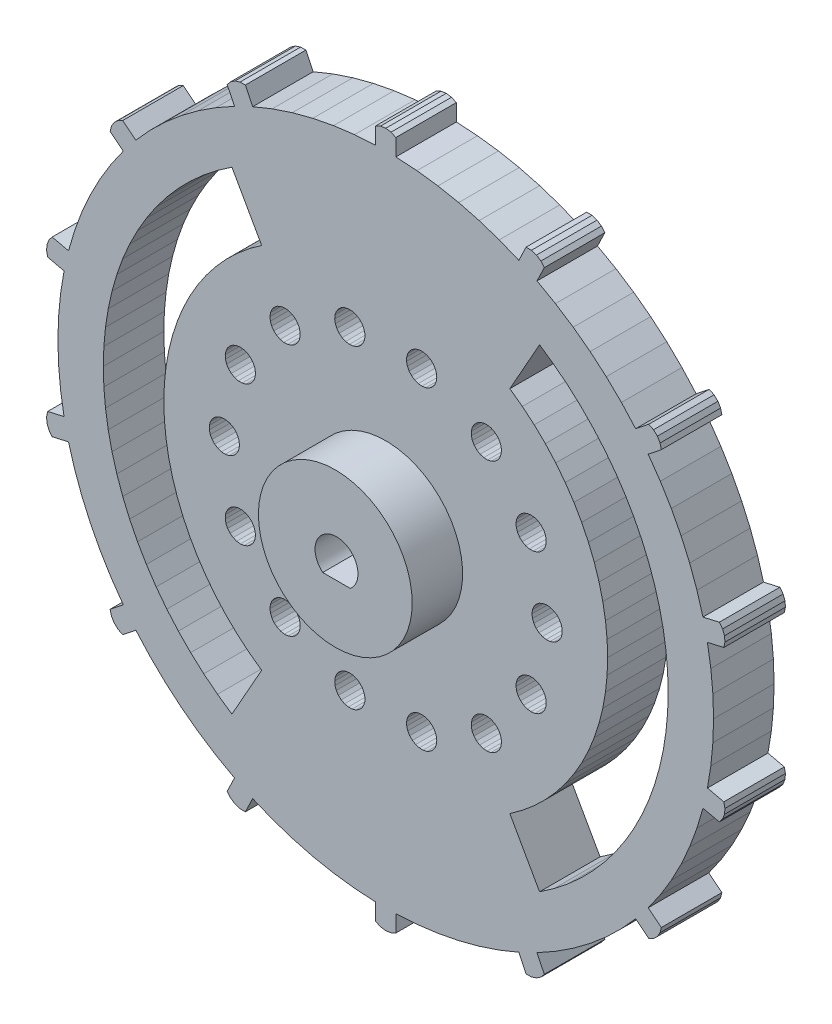
SolidWorks part; units mm, degrees
ref_plane "Front Plane" through (0, 0, 0) normal (0, 0, 1) x (1, 0, 0)
ref_plane "Top Plane" through (0, 0, 0) normal (0, 1, 0) x (1, 0, 0)
ref_plane "Right Plane" through (0, 0, 0) normal (1, 0, 0) x (0, 0, -1)
ref_plane "Plane1" through (0, 0, 6) normal (0, 0, 1) x (1, 0, 0)
sketch "Sketch1" plane through (0, 0, 6) normal (0, 0, 1) x (1, 0, 0)
  line L0 (26.5481, -21.8385) -> (26.9325, -21.478)
  line L1 (26.9325, -21.478) -> (27.1985, -21.023)
  line L2 (27.1985, -21.023) -> (27.3239, -20.5111)
  line L3 (27.3239, -20.5111) -> (26.021, -19.472)
  line L4 (26.021, -19.472) -> (27.2227, -17.7532)
  line L5 (27.2227, -17.7532) -> (28.311, -15.9604)
  line L6 (28.311, -15.9604) -> (29.2815, -14.1012)
  line L7 (29.2815, -14.1012) -> (30.13, -12.1833)
  line L8 (30.13, -12.1833) -> (30.8531, -10.2146)
  line L9 (30.8531, -10.2146) -> (31.4476, -8.2034)
  line L10 (31.4476, -8.2034) -> (33.0724, -8.5743)
  line L11 (33.0724, -8.5743) -> (33.3944, -8.157)
  line L12 (33.3944, -8.157) -> (33.5843, -7.6654)
  line L13 (33.5843, -7.6654) -> (33.6265, -7.1401)
  line L14 (33.6265, -7.1401) -> (33.5174, -6.6244)
  line L15 (33.5174, -6.6244) -> (31.8927, -6.2536)
  line L16 (31.8927, -6.2536) -> (32.2296, -4.1836)
  line L17 (32.2296, -4.1836) -> (32.4323, -2.0962)
  line L18 (32.4323, -2.0962) -> (32.5, 0)
  line L19 (32.5, 0) -> (32.4323, 2.0962)
  line L20 (32.4323, 2.0962) -> (32.2296, 4.1836)
  line L21 (32.2296, 4.1836) -> (31.8927, 6.2536)
  line L22 (31.8927, 6.2536) -> (33.5174, 6.6244)
  line L23 (33.5174, 6.6244) -> (33.6265, 7.1401)
  line L24 (33.6265, 7.1401) -> (33.5843, 7.6654)
  line L25 (33.5843, 7.6654) -> (33.3944, 8.157)
  line L26 (33.3944, 8.157) -> (33.0724, 8.5743)
  line L27 (33.0724, 8.5743) -> (31.4476, 8.2034)
  line L28 (31.4476, 8.2034) -> (30.8531, 10.2146)
  line L29 (30.8531, 10.2146) -> (30.13, 12.1833)
  line L30 (30.13, 12.1833) -> (29.2815, 14.1012)
  line L31 (29.2815, 14.1012) -> (28.311, 15.9604)
  line L32 (28.311, 15.9604) -> (27.2227, 17.7532)
  line L33 (27.2227, 17.7532) -> (26.021, 19.472)
  line L34 (26.021, 19.472) -> (27.3239, 20.5111)
  line L35 (27.3239, 20.5111) -> (27.1985, 21.023)
  line L36 (27.1985, 21.023) -> (26.9325, 21.478)
  line L37 (26.9325, 21.478) -> (26.5481, 21.8385)
  line L38 (26.5481, 21.8385) -> (26.077, 22.0747)
  line L39 (26.077, 22.0747) -> (24.774, 21.0357)
  line L40 (24.774, 21.0357) -> (23.3657, 22.5897)
  line L41 (23.3657, 22.5897) -> (21.8601, 24.0497)
  line L42 (21.8601, 24.0497) -> (20.2634, 25.4095)
  line L43 (20.2634, 25.4095) -> (18.5824, 26.6635)
  line L44 (18.5824, 26.6635) -> (16.824, 27.8065)
  line L45 (16.824, 27.8065) -> (14.9955, 28.8337)
  line L46 (14.9955, 28.8337) -> (15.7186, 30.3353)
  line L47 (15.7186, 30.3353) -> (15.3835, 30.742)
  line L48 (15.3835, 30.742) -> (14.9464, 31.0366)
  line L49 (14.9464, 31.0366) -> (14.4436, 31.1946)
  line L50 (14.4436, 31.1946) -> (13.9167, 31.203)
  line L51 (13.9167, 31.203) -> (13.1936, 29.7015)
  line L52 (13.1936, 29.7015) -> (11.2504, 30.4906)
  line L53 (11.2504, 30.4906) -> (9.2605, 31.1527)
  line L54 (9.2605, 31.1527) -> (7.2319, 31.6852)
  line L55 (7.2319, 31.6852) -> (5.1733, 32.0856)
  line L56 (5.1733, 32.0856) -> (3.0931, 32.3525)
  line L57 (3.0931, 32.3525) -> (1, 32.4846)
  line L58 (1, 32.4846) -> (1, 34.1512)
  line L59 (1, 34.1512) -> (0.5216, 34.3722)
  line L60 (0.5216, 34.3722) -> (0, 34.448)
  line L61 (0, 34.448) -> (-0.5216, 34.3722)
  line L62 (-0.5216, 34.3722) -> (-1, 34.1512)
  line L63 (-1, 34.1512) -> (-1, 32.4846)
  line L64 (-1, 32.4846) -> (-3.0931, 32.3525)
  line L65 (-3.0931, 32.3525) -> (-5.1733, 32.0856)
  line L66 (-5.1733, 32.0856) -> (-7.2319, 31.6852)
  line L67 (-7.2319, 31.6852) -> (-9.2605, 31.1527)
  line L68 (-9.2605, 31.1527) -> (-11.2504, 30.4906)
  line L69 (-11.2504, 30.4906) -> (-13.1936, 29.7015)
  line L70 (-13.1936, 29.7015) -> (-13.9167, 31.203)
  line L71 (-13.9167, 31.203) -> (-14.4436, 31.1946)
  line L72 (-14.4436, 31.1946) -> (-14.9464, 31.0366)
  line L73 (-14.9464, 31.0366) -> (-15.3835, 30.742)
  line L74 (-15.3835, 30.742) -> (-15.7186, 30.3353)
  line L75 (-15.7186, 30.3353) -> (-14.9955, 28.8337)
  line L76 (-14.9955, 28.8337) -> (-16.824, 27.8065)
  line L77 (-16.824, 27.8065) -> (-18.5824, 26.6635)
  line L78 (-18.5824, 26.6635) -> (-20.2634, 25.4095)
  line L79 (-20.2634, 25.4095) -> (-21.8601, 24.0497)
  line L80 (-21.8601, 24.0497) -> (-23.3657, 22.5897)
  line L81 (-23.3657, 22.5897) -> (-24.774, 21.0357)
  line L82 (-24.774, 21.0357) -> (-26.077, 22.0747)
  line L83 (-26.077, 22.0747) -> (-26.5481, 21.8385)
  line L84 (-26.5481, 21.8385) -> (-26.9325, 21.478)
  line L85 (-26.9325, 21.478) -> (-27.1985, 21.023)
  line L86 (-27.1985, 21.023) -> (-27.3239, 20.5111)
  line L87 (-27.3239, 20.5111) -> (-26.021, 19.472)
  line L88 (-26.021, 19.472) -> (-27.2227, 17.7532)
  line L89 (-27.2227, 17.7532) -> (-28.311, 15.9604)
  line L90 (-28.311, 15.9604) -> (-29.2815, 14.1012)
  line L91 (-29.2815, 14.1012) -> (-30.13, 12.1833)
  line L92 (-30.13, 12.1833) -> (-30.8531, 10.2146)
  line L93 (-30.8531, 10.2146) -> (-31.4476, 8.2034)
  line L94 (-31.4476, 8.2034) -> (-33.0724, 8.5743)
  line L95 (-33.0724, 8.5743) -> (-33.3944, 8.157)
  line L96 (-33.3944, 8.157) -> (-33.5843, 7.6654)
  line L97 (-33.5843, 7.6654) -> (-33.6265, 7.1401)
  line L98 (-33.6265, 7.1401) -> (-33.5174, 6.6244)
  line L99 (-33.5174, 6.6244) -> (-31.8927, 6.2536)
  line L100 (-31.8927, 6.2536) -> (-32.2296, 4.1836)
  line L101 (-32.2296, 4.1836) -> (-32.4323, 2.0962)
  line L102 (-32.4323, 2.0962) -> (-32.5, 0)
  line L103 (-32.5, 0) -> (-32.4323, -2.0962)
  line L104 (-32.4323, -2.0962) -> (-32.2296, -4.1836)
  line L105 (-32.2296, -4.1836) -> (-31.8927, -6.2536)
  line L106 (-31.8927, -6.2536) -> (-33.5174, -6.6244)
  line L107 (-33.5174, -6.6244) -> (-33.6265, -7.1401)
  line L108 (-33.6265, -7.1401) -> (-33.5843, -7.6654)
  line L109 (-33.5843, -7.6654) -> (-33.3944, -8.157)
  line L110 (-33.3944, -8.157) -> (-33.0724, -8.5743)
  line L111 (-33.0724, -8.5743) -> (-31.4476, -8.2034)
  line L112 (-31.4476, -8.2034) -> (-30.8531, -10.2146)
  line L113 (-30.8531, -10.2146) -> (-30.13, -12.1833)
  line L114 (-30.13, -12.1833) -> (-29.2815, -14.1012)
  line L115 (-29.2815, -14.1012) -> (-28.311, -15.9604)
  line L116 (-28.311, -15.9604) -> (-27.2227, -17.7532)
  line L117 (-27.2227, -17.7532) -> (-26.021, -19.472)
  line L118 (-26.021, -19.472) -> (-27.3239, -20.5111)
  line L119 (-27.3239, -20.5111) -> (-27.1985, -21.023)
  line L120 (-27.1985, -21.023) -> (-26.9325, -21.478)
  line L121 (-26.9325, -21.478) -> (-26.5481, -21.8385)
  line L122 (-26.5481, -21.8385) -> (-26.077, -22.0747)
  line L123 (-26.077, -22.0747) -> (-24.774, -21.0357)
  line L124 (-24.774, -21.0357) -> (-23.3657, -22.5897)
  line L125 (-23.3657, -22.5897) -> (-21.8601, -24.0497)
  line L126 (-21.8601, -24.0497) -> (-20.2634, -25.4095)
  line L127 (-20.2634, -25.4095) -> (-18.5824, -26.6635)
  line L128 (-18.5824, -26.6635) -> (-16.824, -27.8065)
  line L129 (-16.824, -27.8065) -> (-14.9955, -28.8337)
  line L130 (-14.9955, -28.8337) -> (-15.7186, -30.3353)
  line L131 (-15.7186, -30.3353) -> (-15.3835, -30.742)
  line L132 (-15.3835, -30.742) -> (-14.9464, -31.0366)
  line L133 (-14.9464, -31.0366) -> (-14.4436, -31.1946)
  line L134 (-14.4436, -31.1946) -> (-13.9167, -31.203)
  line L135 (-13.9167, -31.203) -> (-13.1936, -29.7015)
  line L136 (-13.1936, -29.7015) -> (-11.2504, -30.4906)
  line L137 (-11.2504, -30.4906) -> (-9.2605, -31.1527)
  line L138 (-9.2605, -31.1527) -> (-7.2319, -31.6852)
  line L139 (-7.2319, -31.6852) -> (-5.1733, -32.0856)
  line L140 (-5.1733, -32.0856) -> (-3.0931, -32.3525)
  line L141 (-3.0931, -32.3525) -> (-1, -32.4846)
  line L142 (-1, -32.4846) -> (-1, -34.1512)
  line L143 (-1, -34.1512) -> (-0.5216, -34.3722)
  line L144 (-0.5216, -34.3722) -> (0, -34.448)
  line L145 (0, -34.448) -> (0.5216, -34.3722)
  line L146 (0.5216, -34.3722) -> (1, -34.1512)
  line L147 (1, -34.1512) -> (1, -32.4846)
  line L148 (1, -32.4846) -> (3.0931, -32.3525)
  line L149 (3.0931, -32.3525) -> (5.1733, -32.0856)
  line L150 (5.1733, -32.0856) -> (7.2319, -31.6852)
  line L151 (7.2319, -31.6852) -> (9.2605, -31.1527)
  line L152 (9.2605, -31.1527) -> (11.2504, -30.4906)
  line L153 (11.2504, -30.4906) -> (13.1936, -29.7015)
  line L154 (13.1936, -29.7015) -> (13.9167, -31.203)
  line L155 (13.9167, -31.203) -> (14.4436, -31.1946)
  line L156 (14.4436, -31.1946) -> (14.9464, -31.0366)
  line L157 (14.9464, -31.0366) -> (15.3835, -30.742)
  line L158 (15.3835, -30.742) -> (15.7186, -30.3353)
  line L159 (15.7186, -30.3353) -> (14.9955, -28.8337)
  line L160 (14.9955, -28.8337) -> (16.824, -27.8065)
  line L161 (16.824, -27.8065) -> (18.5824, -26.6635)
  line L162 (18.5824, -26.6635) -> (20.2634, -25.4095)
  line L163 (20.2634, -25.4095) -> (21.8601, -24.0497)
  line L164 (21.8601, -24.0497) -> (23.3657, -22.5897)
  line L165 (23.3657, -22.5897) -> (24.774, -21.0357)
  line L166 (24.774, -21.0357) -> (26.077, -22.0747)
  line L167 (26.077, -22.0747) -> (26.5481, -21.8385)
extrude "Boss-Extrude1" add sketch "Sketch1" against normal blind 6
sketch "Sketch2" plane through (0, 0, 6) normal (0, 0, 1) x (1, 0, 0)
  line L0 (23.7291, -14.8636) -> (24.6069, -13.3604)
  line L1 (24.6069, -13.3604) -> (25.3895, -11.8056)
  line L2 (25.3895, -11.8056) -> (26.074, -10.2052)
  line L3 (26.074, -10.2052) -> (26.6578, -8.5653)
  line L4 (26.6578, -8.5653) -> (27.1385, -6.8923)
  line L5 (27.1385, -6.8923) -> (27.5143, -5.1927)
  line L6 (27.5143, -5.1927) -> (27.7838, -3.473)
  line L7 (27.7838, -3.473) -> (27.9459, -1.7398)
  line L8 (27.9459, -1.7398) -> (28, 0)
  line L9 (28, 0) -> (27.9459, 1.7398)
  line L10 (27.9459, 1.7398) -> (27.7838, 3.473)
  line L11 (27.7838, 3.473) -> (27.5143, 5.1927)
  line L12 (27.5143, 5.1927) -> (27.1385, 6.8923)
  line L13 (27.1385, 6.8923) -> (26.6578, 8.5653)
  line L14 (26.6578, 8.5653) -> (26.074, 10.2052)
  line L15 (26.074, 10.2052) -> (25.3895, 11.8056)
  line L16 (25.3895, 11.8056) -> (24.6069, 13.3604)
  line L17 (24.6069, 13.3604) -> (23.7291, 14.8636)
  line L18 (23.7291, 14.8636) -> (22.7597, 16.3094)
  line L19 (22.7597, 16.3094) -> (21.7023, 17.6921)
  line L20 (21.7023, 17.6921) -> (20.561, 19.0064)
  line L21 (20.561, 19.0064) -> (19.3403, 20.2473)
  line L22 (19.3403, 20.2473) -> (18.0448, 21.4099)
  line L23 (18.0448, 21.4099) -> (16.6796, 22.4898)
  line L24 (16.6796, 22.4898) -> (15.2499, 23.4828)
  line L25 (15.2499, 23.4828) -> (12.3022, 18.2388)
  line L26 (12.3022, 18.2388) -> (13.5446, 17.3362)
  line L27 (13.5446, 17.3362) -> (14.7209, 16.3492)
  line L28 (14.7209, 16.3492) -> (15.8255, 15.2825)
  line L29 (15.8255, 15.2825) -> (16.853, 14.1413)
  line L30 (16.853, 14.1413) -> (17.7984, 12.9313)
  line L31 (17.7984, 12.9313) -> (18.6571, 11.6582)
  line L32 (18.6571, 11.6582) -> (19.4248, 10.3284)
  line L33 (19.4248, 10.3284) -> (20.098, 8.9482)
  line L34 (20.098, 8.9482) -> (20.6732, 7.5244)
  line L35 (20.6732, 7.5244) -> (21.1478, 6.064)
  line L36 (21.1478, 6.064) -> (21.5192, 4.5741)
  line L37 (21.5192, 4.5741) -> (21.7859, 3.0618)
  line L38 (21.7859, 3.0618) -> (21.9464, 1.5346)
  line L39 (21.9464, 1.5346) -> (22, 0)
  line L40 (22, 0) -> (21.9464, -1.5346)
  line L41 (21.9464, -1.5346) -> (21.7859, -3.0618)
  line L42 (21.7859, -3.0618) -> (21.5192, -4.5741)
  line L43 (21.5192, -4.5741) -> (21.1478, -6.064)
  line L44 (21.1478, -6.064) -> (20.6732, -7.5244)
  line L45 (20.6732, -7.5244) -> (20.098, -8.9482)
  line L46 (20.098, -8.9482) -> (19.4248, -10.3284)
  line L47 (19.4248, -10.3284) -> (18.6571, -11.6582)
  line L48 (18.6571, -11.6582) -> (17.7984, -12.9313)
  line L49 (17.7984, -12.9313) -> (16.853, -14.1413)
  line L50 (16.853, -14.1413) -> (15.8255, -15.2825)
  line L51 (15.8255, -15.2825) -> (14.7209, -16.3492)
  line L52 (14.7209, -16.3492) -> (13.5446, -17.3362)
  line L53 (13.5446, -17.3362) -> (12.3022, -18.2388)
  line L54 (12.3022, -18.2388) -> (15.2499, -23.4828)
  line L55 (15.2499, -23.4828) -> (16.6796, -22.4898)
  line L56 (16.6796, -22.4898) -> (18.0448, -21.4099)
  line L57 (18.0448, -21.4099) -> (19.3403, -20.2473)
  line L58 (19.3403, -20.2473) -> (20.561, -19.0064)
  line L59 (20.561, -19.0064) -> (21.7023, -17.6921)
  line L60 (21.7023, -17.6921) -> (22.7597, -16.3094)
  line L61 (22.7597, -16.3094) -> (23.7291, -14.8636)
extrude "Cut-Extrude1" cut sketch "Sketch2" against normal through all
sketch "Sketch3" plane through (0, 0, 6) normal (0, 0, 1) x (1, 0, 0)
  line L0 (4.0748, -17.0079) -> (4.409, -16.8357)
  line L1 (4.409, -16.8357) -> (4.6899, -16.5858)
  line L2 (4.6899, -16.5858) -> (4.8999, -16.2738)
  line L3 (4.8999, -16.2738) -> (5.0257, -15.9195)
  line L4 (5.0257, -15.9195) -> (5.0594, -15.545)
  line L5 (5.0594, -15.545) -> (4.9989, -15.1739)
  line L6 (4.9989, -15.1739) -> (4.848, -14.8295)
  line L7 (4.848, -14.8295) -> (4.6162, -14.5334)
  line L8 (4.6162, -14.5334) -> (4.3181, -14.3043)
  line L9 (4.3181, -14.3043) -> (3.9724, -14.1565)
  line L10 (3.9724, -14.1565) -> (3.6007, -14.0994)
  line L11 (3.6007, -14.0994) -> (3.2266, -14.1365)
  line L12 (3.2266, -14.1365) -> (2.8734, -14.2654)
  line L13 (2.8734, -14.2654) -> (2.5633, -14.4781)
  line L14 (2.5633, -14.4781) -> (2.3159, -14.7613)
  line L15 (2.3159, -14.7613) -> (2.1467, -15.0971)
  line L16 (2.1467, -15.0971) -> (2.0664, -15.4644)
  line L17 (2.0664, -15.4644) -> (2.0799, -15.8401)
  line L18 (2.0799, -15.8401) -> (2.1864, -16.2007)
  line L19 (2.1864, -16.2007) -> (2.3792, -16.5235)
  line L20 (2.3792, -16.5235) -> (2.6463, -16.7882)
  line L21 (2.6463, -16.7882) -> (2.9708, -16.9781)
  line L22 (2.9708, -16.9781) -> (3.3323, -17.0814)
  line L23 (3.3323, -17.0814) -> (3.7082, -17.0915)
  line L24 (3.7082, -17.0915) -> (4.0748, -17.0079)
extrude "Cut-Extrude2" cut sketch "Sketch3" against normal through all
sketch "Sketch4" plane through (0, 0, 6) normal (0, 0, 1) x (1, 0, 0)
  line L0 (-2.3792, -16.5235) -> (-2.1864, -16.2007)
  line L1 (-2.1864, -16.2007) -> (-2.0799, -15.8401)
  line L2 (-2.0799, -15.8401) -> (-2.0664, -15.4644)
  line L3 (-2.0664, -15.4644) -> (-2.1467, -15.0971)
  line L4 (-2.1467, -15.0971) -> (-2.3159, -14.7613)
  line L5 (-2.3159, -14.7613) -> (-2.5633, -14.4781)
  line L6 (-2.5633, -14.4781) -> (-2.8734, -14.2654)
  line L7 (-2.8734, -14.2654) -> (-3.2266, -14.1365)
  line L8 (-3.2266, -14.1365) -> (-3.6007, -14.0994)
  line L9 (-3.6007, -14.0994) -> (-3.9724, -14.1565)
  line L10 (-3.9724, -14.1565) -> (-4.3181, -14.3043)
  line L11 (-4.3181, -14.3043) -> (-4.6162, -14.5334)
  line L12 (-4.6162, -14.5334) -> (-4.848, -14.8295)
  line L13 (-4.848, -14.8295) -> (-4.9989, -15.1739)
  line L14 (-4.9989, -15.1739) -> (-5.0594, -15.545)
  line L15 (-5.0594, -15.545) -> (-5.0257, -15.9195)
  line L16 (-5.0257, -15.9195) -> (-4.8999, -16.2738)
  line L17 (-4.8999, -16.2738) -> (-4.6899, -16.5858)
  line L18 (-4.6899, -16.5858) -> (-4.409, -16.8357)
  line L19 (-4.409, -16.8357) -> (-4.0748, -17.0079)
  line L20 (-4.0748, -17.0079) -> (-3.7082, -17.0915)
  line L21 (-3.7082, -17.0915) -> (-3.3323, -17.0814)
  line L22 (-3.3323, -17.0814) -> (-2.9708, -16.9781)
  line L23 (-2.9708, -16.9781) -> (-2.6463, -16.7882)
  line L24 (-2.6463, -16.7882) -> (-2.3792, -16.5235)
extrude "Cut-Extrude3" cut sketch "Sketch4" against normal through all
sketch "Sketch5" plane through (0, 0, 6) normal (0, 0, 1) x (1, 0, 0)
  line L0 (-11.4218, -12.9084) -> (-11.2771, -13.2554)
  line L1 (-11.2771, -13.2554) -> (-11.0507, -13.5556)
  line L2 (-11.0507, -13.5556) -> (-10.7567, -13.79)
  line L3 (-10.7567, -13.79) -> (-10.4137, -13.944)
  line L4 (-10.4137, -13.944) -> (-10.0431, -14.0078)
  line L5 (-10.0431, -14.0078) -> (-9.6684, -13.9775)
  line L6 (-9.6684, -13.9775) -> (-9.3129, -13.8549)
  line L7 (-9.3129, -13.8549) -> (-8.9991, -13.6477)
  line L8 (-8.9991, -13.6477) -> (-8.7467, -13.3691)
  line L9 (-8.7467, -13.3691) -> (-8.5715, -13.0364)
  line L10 (-8.5715, -13.0364) -> (-8.4845, -12.6706)
  line L11 (-8.4845, -12.6706) -> (-8.4913, -12.2946)
  line L12 (-8.4913, -12.2946) -> (-8.5913, -11.9322)
  line L13 (-8.5913, -11.9322) -> (-8.7783, -11.606)
  line L14 (-8.7783, -11.606) -> (-9.0406, -11.3366)
  line L15 (-9.0406, -11.3366) -> (-9.3616, -11.1408)
  line L16 (-9.3616, -11.1408) -> (-9.7213, -11.0311)
  line L17 (-9.7213, -11.0311) -> (-10.0969, -11.0142)
  line L18 (-10.0969, -11.0142) -> (-10.4649, -11.0913)
  line L19 (-10.4649, -11.0913) -> (-10.8022, -11.2574)
  line L20 (-10.8022, -11.2574) -> (-11.0875, -11.5023)
  line L21 (-11.0875, -11.5023) -> (-11.3031, -11.8104)
  line L22 (-11.3031, -11.8104) -> (-11.4352, -12.1624)
  line L23 (-11.4352, -12.1624) -> (-11.4756, -12.5362)
  line L24 (-11.4756, -12.5362) -> (-11.4218, -12.9084)
extrude "Cut-Extrude4" cut sketch "Sketch5" against normal through all
sketch "Sketch6" plane through (0, 0, 6) normal (0, 0, 1) x (1, 0, 0)
  line L0 (-20.6732, -7.5244) -> (-21.1478, -6.064)
  line L1 (-21.1478, -6.064) -> (-21.5192, -4.5741)
  line L2 (-21.5192, -4.5741) -> (-21.7859, -3.0618)
  line L3 (-21.7859, -3.0618) -> (-21.9464, -1.5346)
  line L4 (-21.9464, -1.5346) -> (-22, 0)
  line L5 (-22, 0) -> (-21.9464, 1.5346)
  line L6 (-21.9464, 1.5346) -> (-21.7859, 3.0618)
  line L7 (-21.7859, 3.0618) -> (-21.5192, 4.5741)
  line L8 (-21.5192, 4.5741) -> (-21.1478, 6.064)
  line L9 (-21.1478, 6.064) -> (-20.6732, 7.5244)
  line L10 (-20.6732, 7.5244) -> (-20.098, 8.9482)
  line L11 (-20.098, 8.9482) -> (-19.4248, 10.3284)
  line L12 (-19.4248, 10.3284) -> (-18.6571, 11.6582)
  line L13 (-18.6571, 11.6582) -> (-17.7984, 12.9313)
  line L14 (-17.7984, 12.9313) -> (-16.853, 14.1413)
  line L15 (-16.853, 14.1413) -> (-15.8255, 15.2825)
  line L16 (-15.8255, 15.2825) -> (-14.7209, 16.3492)
  line L17 (-14.7209, 16.3492) -> (-13.5446, 17.3362)
  line L18 (-13.5446, 17.3362) -> (-12.3022, 18.2388)
  line L19 (-12.3022, 18.2388) -> (-15.2499, 23.4828)
  line L20 (-15.2499, 23.4828) -> (-16.6796, 22.4898)
  line L21 (-16.6796, 22.4898) -> (-18.0448, 21.4099)
  line L22 (-18.0448, 21.4099) -> (-19.3403, 20.2473)
  line L23 (-19.3403, 20.2473) -> (-20.561, 19.0064)
  line L24 (-20.561, 19.0064) -> (-21.7023, 17.6921)
  line L25 (-21.7023, 17.6921) -> (-22.7597, 16.3094)
  line L26 (-22.7597, 16.3094) -> (-23.7291, 14.8636)
  line L27 (-23.7291, 14.8636) -> (-24.6069, 13.3604)
  line L28 (-24.6069, 13.3604) -> (-25.3895, 11.8056)
  line L29 (-25.3895, 11.8056) -> (-26.074, 10.2052)
  line L30 (-26.074, 10.2052) -> (-26.6578, 8.5653)
  line L31 (-26.6578, 8.5653) -> (-27.1385, 6.8923)
  line L32 (-27.1385, 6.8923) -> (-27.5143, 5.1927)
  line L33 (-27.5143, 5.1927) -> (-27.7838, 3.473)
  line L34 (-27.7838, 3.473) -> (-27.9459, 1.7398)
  line L35 (-27.9459, 1.7398) -> (-28, 0)
  line L36 (-28, 0) -> (-27.9459, -1.7398)
  line L37 (-27.9459, -1.7398) -> (-27.7838, -3.473)
  line L38 (-27.7838, -3.473) -> (-27.5143, -5.1927)
  line L39 (-27.5143, -5.1927) -> (-27.1385, -6.8923)
  line L40 (-27.1385, -6.8923) -> (-26.6578, -8.5653)
  line L41 (-26.6578, -8.5653) -> (-26.074, -10.2052)
  line L42 (-26.074, -10.2052) -> (-25.3895, -11.8056)
  line L43 (-25.3895, -11.8056) -> (-24.6069, -13.3604)
  line L44 (-24.6069, -13.3604) -> (-23.7291, -14.8636)
  line L45 (-23.7291, -14.8636) -> (-22.7597, -16.3094)
  line L46 (-22.7597, -16.3094) -> (-21.7023, -17.6921)
  line L47 (-21.7023, -17.6921) -> (-20.561, -19.0064)
  line L48 (-20.561, -19.0064) -> (-19.3403, -20.2473)
  line L49 (-19.3403, -20.2473) -> (-18.0448, -21.4099)
  line L50 (-18.0448, -21.4099) -> (-16.6796, -22.4898)
  line L51 (-16.6796, -22.4898) -> (-15.2499, -23.4828)
  line L52 (-15.2499, -23.4828) -> (-12.3022, -18.2388)
  line L53 (-12.3022, -18.2388) -> (-13.5446, -17.3362)
  line L54 (-13.5446, -17.3362) -> (-14.7209, -16.3492)
  line L55 (-14.7209, -16.3492) -> (-15.8255, -15.2825)
  line L56 (-15.8255, -15.2825) -> (-16.853, -14.1413)
  line L57 (-16.853, -14.1413) -> (-17.7984, -12.9313)
  line L58 (-17.7984, -12.9313) -> (-18.6571, -11.6582)
  line L59 (-18.6571, -11.6582) -> (-19.4248, -10.3284)
  line L60 (-19.4248, -10.3284) -> (-20.098, -8.9482)
  line L61 (-20.098, -8.9482) -> (-20.6732, -7.5244)
extrude "Cut-Extrude5" cut sketch "Sketch6" against normal through all
sketch "Sketch7" plane through (0, 0, 6) normal (0, 0, 1) x (1, 0, 0)
  line L0 (-15.6747, -7.7572) -> (-15.4325, -8.0448)
  line L1 (-15.4325, -8.0448) -> (-15.1263, -8.263)
  line L2 (-15.1263, -8.263) -> (-14.7755, -8.3983)
  line L3 (-14.7755, -8.3983) -> (-14.402, -8.4421)
  line L4 (-14.402, -8.4421) -> (-14.0294, -8.3916)
  line L5 (-14.0294, -8.3916) -> (-13.6811, -8.2501)
  line L6 (-13.6811, -8.2501) -> (-13.3789, -8.0263)
  line L7 (-13.3789, -8.0263) -> (-13.1418, -7.7345)
  line L8 (-13.1418, -7.7345) -> (-12.9848, -7.3928)
  line L9 (-12.9848, -7.3928) -> (-12.9177, -7.0229)
  line L10 (-12.9177, -7.0229) -> (-12.9447, -6.6479)
  line L11 (-12.9447, -6.6479) -> (-13.064, -6.2913)
  line L12 (-13.064, -6.2913) -> (-13.2684, -5.9757)
  line L13 (-13.2684, -5.9757) -> (-13.5448, -5.7207)
  line L14 (-13.5448, -5.7207) -> (-13.8759, -5.5426)
  line L15 (-13.8759, -5.5426) -> (-14.2409, -5.4523)
  line L16 (-14.2409, -5.4523) -> (-14.6169, -5.4557)
  line L17 (-14.6169, -5.4557) -> (-14.9802, -5.5525)
  line L18 (-14.9802, -5.5525) -> (-15.308, -5.7366)
  line L19 (-15.308, -5.7366) -> (-15.5798, -5.9964)
  line L20 (-15.5798, -5.9964) -> (-15.7784, -6.3157)
  line L21 (-15.7784, -6.3157) -> (-15.8914, -6.6743)
  line L22 (-15.8914, -6.6743) -> (-15.9116, -7.0498)
  line L23 (-15.9116, -7.0498) -> (-15.8379, -7.4185)
  line L24 (-15.8379, -7.4185) -> (-15.6747, -7.7572)
extrude "Cut-Extrude6" cut sketch "Sketch7" against normal through all
sketch "Sketch8" plane through (0, 0, 6) normal (0, 0, 1) x (1, 0, 0)
  line L0 (11.4352, -12.1624) -> (11.3031, -11.8104)
  line L1 (11.3031, -11.8104) -> (11.0875, -11.5023)
  line L2 (11.0875, -11.5023) -> (10.8022, -11.2574)
  line L3 (10.8022, -11.2574) -> (10.4649, -11.0913)
  line L4 (10.4649, -11.0913) -> (10.0969, -11.0142)
  line L5 (10.0969, -11.0142) -> (9.7213, -11.0311)
  line L6 (9.7213, -11.0311) -> (9.3616, -11.1408)
  line L7 (9.3616, -11.1408) -> (9.0406, -11.3366)
  line L8 (9.0406, -11.3366) -> (8.7783, -11.606)
  line L9 (8.7783, -11.606) -> (8.5913, -11.9322)
  line L10 (8.5913, -11.9322) -> (8.4913, -12.2946)
  line L11 (8.4913, -12.2946) -> (8.4845, -12.6706)
  line L12 (8.4845, -12.6706) -> (8.5715, -13.0364)
  line L13 (8.5715, -13.0364) -> (8.7467, -13.3691)
  line L14 (8.7467, -13.3691) -> (8.9991, -13.6477)
  line L15 (8.9991, -13.6477) -> (9.3129, -13.8549)
  line L16 (9.3129, -13.8549) -> (9.6684, -13.9775)
  line L17 (9.6684, -13.9775) -> (10.0431, -14.0078)
  line L18 (10.0431, -14.0078) -> (10.4137, -13.944)
  line L19 (10.4137, -13.944) -> (10.7567, -13.79)
  line L20 (10.7567, -13.79) -> (11.0507, -13.5556)
  line L21 (11.0507, -13.5556) -> (11.2771, -13.2554)
  line L22 (11.2771, -13.2554) -> (11.4218, -12.9084)
  line L23 (11.4218, -12.9084) -> (11.4756, -12.5362)
  line L24 (11.4756, -12.5362) -> (11.4352, -12.1624)
extrude "Cut-Extrude7" cut sketch "Sketch8" against normal through all
sketch "Sketch9" plane through (0, 0, 6) normal (0, 0, 1) x (1, 0, 0)
  line L0 (14.7755, -8.3983) -> (15.1263, -8.263)
  line L1 (15.1263, -8.263) -> (15.4325, -8.0448)
  line L2 (15.4325, -8.0448) -> (15.6747, -7.7572)
  line L3 (15.6747, -7.7572) -> (15.8379, -7.4185)
  line L4 (15.8379, -7.4185) -> (15.9116, -7.0498)
  line L5 (15.9116, -7.0498) -> (15.8914, -6.6743)
  line L6 (15.8914, -6.6743) -> (15.7784, -6.3157)
  line L7 (15.7784, -6.3157) -> (15.5798, -5.9964)
  line L8 (15.5798, -5.9964) -> (15.308, -5.7366)
  line L9 (15.308, -5.7366) -> (14.9802, -5.5525)
  line L10 (14.9802, -5.5525) -> (14.6169, -5.4557)
  line L11 (14.6169, -5.4557) -> (14.2409, -5.4523)
  line L12 (14.2409, -5.4523) -> (13.8759, -5.5426)
  line L13 (13.8759, -5.5426) -> (13.5448, -5.7207)
  line L14 (13.5448, -5.7207) -> (13.2684, -5.9757)
  line L15 (13.2684, -5.9757) -> (13.064, -6.2913)
  line L16 (13.064, -6.2913) -> (12.9447, -6.6479)
  line L17 (12.9447, -6.6479) -> (12.9177, -7.0229)
  line L18 (12.9177, -7.0229) -> (12.9848, -7.3928)
  line L19 (12.9848, -7.3928) -> (13.1418, -7.7345)
  line L20 (13.1418, -7.7345) -> (13.3789, -8.0263)
  line L21 (13.3789, -8.0263) -> (13.6811, -8.2501)
  line L22 (13.6811, -8.2501) -> (14.0294, -8.3916)
  line L23 (14.0294, -8.3916) -> (14.402, -8.4421)
  line L24 (14.402, -8.4421) -> (14.7755, -8.3983)
extrude "Cut-Extrude8" cut sketch "Sketch9" against normal through all
sketch "Sketch10" plane through (0, 0, 6) normal (0, 0, 1) x (1, 0, 0)
  line L0 (-17.2135, -0.8817) -> (-16.9561, -1.1558)
  line L1 (-16.9561, -1.1558) -> (-16.6387, -1.3572)
  line L2 (-16.6387, -1.3572) -> (-16.2811, -1.4734)
  line L3 (-16.2811, -1.4734) -> (-15.9058, -1.497)
  line L4 (-15.9058, -1.497) -> (-15.5365, -1.4266)
  line L5 (-15.5365, -1.4266) -> (-15.1963, -1.2665)
  line L6 (-15.1963, -1.2665) -> (-14.9065, -1.0268)
  line L7 (-14.9065, -1.0268) -> (-14.6855, -0.7226)
  line L8 (-14.6855, -0.7226) -> (-14.5471, -0.373)
  line L9 (-14.5471, -0.373) -> (-14.5, 0)
  line L10 (-14.5, 0) -> (-14.5471, 0.373)
  line L11 (-14.5471, 0.373) -> (-14.6855, 0.7226)
  line L12 (-14.6855, 0.7226) -> (-14.9065, 1.0268)
  line L13 (-14.9065, 1.0268) -> (-15.1963, 1.2665)
  line L14 (-15.1963, 1.2665) -> (-15.5365, 1.4266)
  line L15 (-15.5365, 1.4266) -> (-15.9058, 1.497)
  line L16 (-15.9058, 1.497) -> (-16.2811, 1.4734)
  line L17 (-16.2811, 1.4734) -> (-16.6387, 1.3572)
  line L18 (-16.6387, 1.3572) -> (-16.9561, 1.1558)
  line L19 (-16.9561, 1.1558) -> (-17.2135, 0.8817)
  line L20 (-17.2135, 0.8817) -> (-17.3947, 0.5522)
  line L21 (-17.3947, 0.5522) -> (-17.4882, 0.188)
  line L22 (-17.4882, 0.188) -> (-17.4882, -0.188)
  line L23 (-17.4882, -0.188) -> (-17.3947, -0.5522)
  line L24 (-17.3947, -0.5522) -> (-17.2135, -0.8817)
extrude "Cut-Extrude9" cut sketch "Sketch10" against normal through all
sketch "Sketch11" plane through (0, 0, 6) normal (0, 0, 1) x (1, 0, 0)
  line L0 (-15.308, 5.7366) -> (-14.9802, 5.5525)
  line L1 (-14.9802, 5.5525) -> (-14.6169, 5.4557)
  line L2 (-14.6169, 5.4557) -> (-14.2409, 5.4523)
  line L3 (-14.2409, 5.4523) -> (-13.8759, 5.5426)
  line L4 (-13.8759, 5.5426) -> (-13.5448, 5.7207)
  line L5 (-13.5448, 5.7207) -> (-13.2684, 5.9757)
  line L6 (-13.2684, 5.9757) -> (-13.064, 6.2913)
  line L7 (-13.064, 6.2913) -> (-12.9447, 6.6479)
  line L8 (-12.9447, 6.6479) -> (-12.9177, 7.0229)
  line L9 (-12.9177, 7.0229) -> (-12.9848, 7.3928)
  line L10 (-12.9848, 7.3928) -> (-13.1418, 7.7345)
  line L11 (-13.1418, 7.7345) -> (-13.3789, 8.0263)
  line L12 (-13.3789, 8.0263) -> (-13.6811, 8.2501)
  line L13 (-13.6811, 8.2501) -> (-14.0294, 8.3916)
  line L14 (-14.0294, 8.3916) -> (-14.402, 8.4421)
  line L15 (-14.402, 8.4421) -> (-14.7755, 8.3983)
  line L16 (-14.7755, 8.3983) -> (-15.1263, 8.263)
  line L17 (-15.1263, 8.263) -> (-15.4325, 8.0448)
  line L18 (-15.4325, 8.0448) -> (-15.6747, 7.7572)
  line L19 (-15.6747, 7.7572) -> (-15.8379, 7.4185)
  line L20 (-15.8379, 7.4185) -> (-15.9116, 7.0498)
  line L21 (-15.9116, 7.0498) -> (-15.8914, 6.6743)
  line L22 (-15.8914, 6.6743) -> (-15.7784, 6.3157)
  line L23 (-15.7784, 6.3157) -> (-15.5798, 5.9964)
  line L24 (-15.5798, 5.9964) -> (-15.308, 5.7366)
extrude "Cut-Extrude10" cut sketch "Sketch11" against normal through all
sketch "Sketch12" plane through (0, 0, 6) normal (0, 0, 1) x (1, 0, 0)
  line L0 (16.2811, -1.4734) -> (16.6387, -1.3572)
  line L1 (16.6387, -1.3572) -> (16.9561, -1.1558)
  line L2 (16.9561, -1.1558) -> (17.2135, -0.8817)
  line L3 (17.2135, -0.8817) -> (17.3947, -0.5522)
  line L4 (17.3947, -0.5522) -> (17.4882, -0.188)
  line L5 (17.4882, -0.188) -> (17.4882, 0.188)
  line L6 (17.4882, 0.188) -> (17.3947, 0.5522)
  line L7 (17.3947, 0.5522) -> (17.2135, 0.8817)
  line L8 (17.2135, 0.8817) -> (16.9561, 1.1558)
  line L9 (16.9561, 1.1558) -> (16.6387, 1.3572)
  line L10 (16.6387, 1.3572) -> (16.2811, 1.4734)
  line L11 (16.2811, 1.4734) -> (15.9058, 1.497)
  line L12 (15.9058, 1.497) -> (15.5365, 1.4266)
  line L13 (15.5365, 1.4266) -> (15.1963, 1.2665)
  line L14 (15.1963, 1.2665) -> (14.9065, 1.0268)
  line L15 (14.9065, 1.0268) -> (14.6855, 0.7226)
  line L16 (14.6855, 0.7226) -> (14.5471, 0.373)
  line L17 (14.5471, 0.373) -> (14.5, 0)
  line L18 (14.5, 0) -> (14.5471, -0.373)
  line L19 (14.5471, -0.373) -> (14.6855, -0.7226)
  line L20 (14.6855, -0.7226) -> (14.9065, -1.0268)
  line L21 (14.9065, -1.0268) -> (15.1963, -1.2665)
  line L22 (15.1963, -1.2665) -> (15.5365, -1.4266)
  line L23 (15.5365, -1.4266) -> (15.9058, -1.497)
  line L24 (15.9058, -1.497) -> (16.2811, -1.4734)
extrude "Cut-Extrude11" cut sketch "Sketch12" against normal through all
sketch "Sketch13" plane through (0, 0, 6) normal (0, 0, 1) x (1, 0, 0)
  line L0 (15.308, 5.7366) -> (15.5798, 5.9964)
  line L1 (15.5798, 5.9964) -> (15.7784, 6.3157)
  line L2 (15.7784, 6.3157) -> (15.8914, 6.6743)
  line L3 (15.8914, 6.6743) -> (15.9116, 7.0498)
  line L4 (15.9116, 7.0498) -> (15.8379, 7.4185)
  line L5 (15.8379, 7.4185) -> (15.6747, 7.7572)
  line L6 (15.6747, 7.7572) -> (15.4325, 8.0448)
  line L7 (15.4325, 8.0448) -> (15.1263, 8.263)
  line L8 (15.1263, 8.263) -> (14.7755, 8.3983)
  line L9 (14.7755, 8.3983) -> (14.402, 8.4421)
  line L10 (14.402, 8.4421) -> (14.0294, 8.3916)
  line L11 (14.0294, 8.3916) -> (13.6811, 8.2501)
  line L12 (13.6811, 8.2501) -> (13.3789, 8.0263)
  line L13 (13.3789, 8.0263) -> (13.1418, 7.7345)
  line L14 (13.1418, 7.7345) -> (12.9848, 7.3928)
  line L15 (12.9848, 7.3928) -> (12.9177, 7.0229)
  line L16 (12.9177, 7.0229) -> (12.9447, 6.6479)
  line L17 (12.9447, 6.6479) -> (13.064, 6.2913)
  line L18 (13.064, 6.2913) -> (13.2684, 5.9757)
  line L19 (13.2684, 5.9757) -> (13.5448, 5.7207)
  line L20 (13.5448, 5.7207) -> (13.8759, 5.5426)
  line L21 (13.8759, 5.5426) -> (14.2409, 5.4523)
  line L22 (14.2409, 5.4523) -> (14.6169, 5.4557)
  line L23 (14.6169, 5.4557) -> (14.9802, 5.5525)
  line L24 (14.9802, 5.5525) -> (15.308, 5.7366)
extrude "Cut-Extrude12" cut sketch "Sketch13" against normal through all
sketch "Sketch14" plane through (0, 0, 6) normal (0, 0, 1) x (1, 0, 0)
  line L0 (-10.0969, 11.0142) -> (-9.7213, 11.0311)
  line L1 (-9.7213, 11.0311) -> (-9.3616, 11.1408)
  line L2 (-9.3616, 11.1408) -> (-9.0406, 11.3366)
  line L3 (-9.0406, 11.3366) -> (-8.7783, 11.606)
  line L4 (-8.7783, 11.606) -> (-8.5913, 11.9322)
  line L5 (-8.5913, 11.9322) -> (-8.4913, 12.2946)
  line L6 (-8.4913, 12.2946) -> (-8.4845, 12.6706)
  line L7 (-8.4845, 12.6706) -> (-8.5715, 13.0364)
  line L8 (-8.5715, 13.0364) -> (-8.7467, 13.3691)
  line L9 (-8.7467, 13.3691) -> (-8.9991, 13.6477)
  line L10 (-8.9991, 13.6477) -> (-9.3129, 13.8549)
  line L11 (-9.3129, 13.8549) -> (-9.6684, 13.9775)
  line L12 (-9.6684, 13.9775) -> (-10.0431, 14.0078)
  line L13 (-10.0431, 14.0078) -> (-10.4137, 13.944)
  line L14 (-10.4137, 13.944) -> (-10.7567, 13.79)
  line L15 (-10.7567, 13.79) -> (-11.0507, 13.5556)
  line L16 (-11.0507, 13.5556) -> (-11.2771, 13.2554)
  line L17 (-11.2771, 13.2554) -> (-11.4218, 12.9084)
  line L18 (-11.4218, 12.9084) -> (-11.4756, 12.5362)
  line L19 (-11.4756, 12.5362) -> (-11.4352, 12.1624)
  line L20 (-11.4352, 12.1624) -> (-11.3031, 11.8104)
  line L21 (-11.3031, 11.8104) -> (-11.0875, 11.5023)
  line L22 (-11.0875, 11.5023) -> (-10.8022, 11.2574)
  line L23 (-10.8022, 11.2574) -> (-10.4649, 11.0913)
  line L24 (-10.4649, 11.0913) -> (-10.0969, 11.0142)
extrude "Cut-Extrude13" cut sketch "Sketch14" against normal through all
sketch "Sketch15" plane through (0, 0, 6) normal (0, 0, 1) x (1, 0, 0)
  line L0 (8.7783, 11.606) -> (9.0406, 11.3366)
  line L1 (9.0406, 11.3366) -> (9.3616, 11.1408)
  line L2 (9.3616, 11.1408) -> (9.7213, 11.0311)
  line L3 (9.7213, 11.0311) -> (10.0969, 11.0142)
  line L4 (10.0969, 11.0142) -> (10.4649, 11.0913)
  line L5 (10.4649, 11.0913) -> (10.8022, 11.2574)
  line L6 (10.8022, 11.2574) -> (11.0875, 11.5023)
  line L7 (11.0875, 11.5023) -> (11.3031, 11.8104)
  line L8 (11.3031, 11.8104) -> (11.4352, 12.1624)
  line L9 (11.4352, 12.1624) -> (11.4756, 12.5362)
  line L10 (11.4756, 12.5362) -> (11.4218, 12.9084)
  line L11 (11.4218, 12.9084) -> (11.2771, 13.2554)
  line L12 (11.2771, 13.2554) -> (11.0507, 13.5556)
  line L13 (11.0507, 13.5556) -> (10.7567, 13.79)
  line L14 (10.7567, 13.79) -> (10.4137, 13.944)
  line L15 (10.4137, 13.944) -> (10.0431, 14.0078)
  line L16 (10.0431, 14.0078) -> (9.6684, 13.9775)
  line L17 (9.6684, 13.9775) -> (9.3129, 13.8549)
  line L18 (9.3129, 13.8549) -> (8.9991, 13.6477)
  line L19 (8.9991, 13.6477) -> (8.7467, 13.3691)
  line L20 (8.7467, 13.3691) -> (8.5715, 13.0364)
  line L21 (8.5715, 13.0364) -> (8.4845, 12.6706)
  line L22 (8.4845, 12.6706) -> (8.4913, 12.2946)
  line L23 (8.4913, 12.2946) -> (8.5913, 11.9322)
  line L24 (8.5913, 11.9322) -> (8.7783, 11.606)
extrude "Cut-Extrude14" cut sketch "Sketch15" against normal through all
sketch "Sketch16" plane through (0, 0, 6) normal (0, 0, 1) x (1, 0, 0)
  line L0 (-3.6007, 14.0994) -> (-3.2266, 14.1365)
  line L1 (-3.2266, 14.1365) -> (-2.8734, 14.2654)
  line L2 (-2.8734, 14.2654) -> (-2.5633, 14.4781)
  line L3 (-2.5633, 14.4781) -> (-2.3159, 14.7613)
  line L4 (-2.3159, 14.7613) -> (-2.1467, 15.0971)
  line L5 (-2.1467, 15.0971) -> (-2.0664, 15.4644)
  line L6 (-2.0664, 15.4644) -> (-2.0799, 15.8401)
  line L7 (-2.0799, 15.8401) -> (-2.1864, 16.2007)
  line L8 (-2.1864, 16.2007) -> (-2.3792, 16.5235)
  line L9 (-2.3792, 16.5235) -> (-2.6463, 16.7882)
  line L10 (-2.6463, 16.7882) -> (-2.9708, 16.9781)
  line L11 (-2.9708, 16.9781) -> (-3.3323, 17.0814)
  line L12 (-3.3323, 17.0814) -> (-3.7082, 17.0915)
  line L13 (-3.7082, 17.0915) -> (-4.0748, 17.0079)
  line L14 (-4.0748, 17.0079) -> (-4.409, 16.8357)
  line L15 (-4.409, 16.8357) -> (-4.6899, 16.5858)
  line L16 (-4.6899, 16.5858) -> (-4.8999, 16.2738)
  line L17 (-4.8999, 16.2738) -> (-5.0257, 15.9195)
  line L18 (-5.0257, 15.9195) -> (-5.0594, 15.545)
  line L19 (-5.0594, 15.545) -> (-4.9989, 15.1739)
  line L20 (-4.9989, 15.1739) -> (-4.848, 14.8295)
  line L21 (-4.848, 14.8295) -> (-4.6162, 14.5334)
  line L22 (-4.6162, 14.5334) -> (-4.3181, 14.3043)
  line L23 (-4.3181, 14.3043) -> (-3.9724, 14.1565)
  line L24 (-3.9724, 14.1565) -> (-3.6007, 14.0994)
extrude "Cut-Extrude15" cut sketch "Sketch16" against normal through all
sketch "Sketch17" plane through (0, 0, 0) normal (0, 0, -1) x (-1, 0, 0)
  line L0 (-3.6007, 14.0994) -> (-3.2266, 14.1365)
  line L1 (-3.2266, 14.1365) -> (-2.8734, 14.2654)
  line L2 (-2.8734, 14.2654) -> (-2.5633, 14.4781)
  line L3 (-2.5633, 14.4781) -> (-2.3159, 14.7613)
  line L4 (-2.3159, 14.7613) -> (-2.1467, 15.0971)
  line L5 (-2.1467, 15.0971) -> (-2.0664, 15.4644)
  line L6 (-2.0664, 15.4644) -> (-2.0799, 15.8401)
  line L7 (-2.0799, 15.8401) -> (-2.1864, 16.2007)
  line L8 (-2.1864, 16.2007) -> (-2.3792, 16.5235)
  line L9 (-2.3792, 16.5235) -> (-2.6463, 16.7882)
  line L10 (-2.6463, 16.7882) -> (-2.9708, 16.9781)
  line L11 (-2.9708, 16.9781) -> (-3.3323, 17.0814)
  line L12 (-3.3323, 17.0814) -> (-3.7082, 17.0915)
  line L13 (-3.7082, 17.0915) -> (-4.0748, 17.0079)
  line L14 (-4.0748, 17.0079) -> (-4.409, 16.8357)
  line L15 (-4.409, 16.8357) -> (-4.6899, 16.5858)
  line L16 (-4.6899, 16.5858) -> (-4.8999, 16.2738)
  line L17 (-4.8999, 16.2738) -> (-5.0257, 15.9195)
  line L18 (-5.0257, 15.9195) -> (-5.0594, 15.545)
  line L19 (-5.0594, 15.545) -> (-4.9989, 15.1739)
  line L20 (-4.9989, 15.1739) -> (-4.848, 14.8295)
  line L21 (-4.848, 14.8295) -> (-4.6162, 14.5334)
  line L22 (-4.6162, 14.5334) -> (-4.3181, 14.3043)
  line L23 (-4.3181, 14.3043) -> (-3.9724, 14.1565)
  line L24 (-3.9724, 14.1565) -> (-3.6007, 14.0994)
extrude "Cut-Extrude16" cut sketch "Sketch17" against normal through all
sketch "Sketch18" plane through (0, 0, 0) normal (0, 0, -1) x (-1, 0, 0)
  circle A0 centre (0, 0) radius 8 construction
  circle A1 centre (0, 0) radius 8.127
  point P0 (0, 0)
  dimension "D1" = 16
  dimension "D2" = 0.127
extrude "Cut-Extrude17" cut sketch "Sketch18" against normal blind 3.5
sketch "Sketch19" plane through (0, 0, 6) normal (0, 0, 1) x (1, 0, 0)
  circle A0 centre (0, 0) radius 7.75 construction
  circle A1 centre (0, 0) radius 7.623
  dimension "D1" = 15.5
  dimension "D2" = 0.127
extrude "Boss-Extrude2" add sketch "Sketch19" along normal blind 5
sketch "Sketch20" plane through (0, 0, 11) normal (0, 0, 1) x (1, 0, 0)
  line L0 (1.489, -1.8171) -> (-1.2511, -1.8171)
  line L14 (1.4418, -1.6901) -> (-1.2039, -1.6901) construction
  line L15 (1.4418, -1.6901) -> (-1.2039, -1.6901) construction
  arc A0 (1.4418, -1.6901) -> (-1.2039, -1.6901) centre (0.1189, -0.1901) ccw construction
  arc A1 (1.4418, -1.6901) -> (-1.2039, -1.6901) centre (0.1189, -0.1901) ccw construction
  arc A2 (1.489, -1.8171) -> (-1.2511, -1.8171) centre (0.1189, -0.1901) ccw
  dimension "D1" = 0.127
extrude "Cut-Extrude18" cut sketch "Sketch20" against normal blind 7
